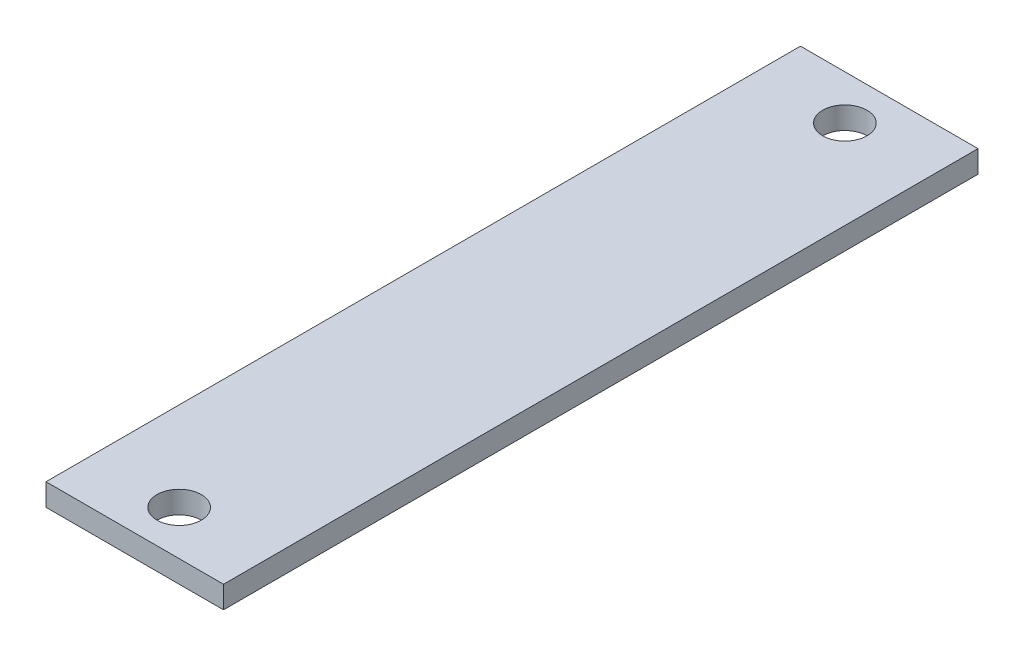
SolidWorks part; units mm, degrees
ref_plane "Front Plane" through (0, 0, 0) normal (0, 0, 1) x (1, 0, 0)
ref_plane "Top Plane" through (0, 0, 0) normal (0, 1, 0) x (1, 0, 0)
ref_plane "Right Plane" through (0, 0, 0) normal (1, 0, 0) x (0, 0, -1)
ref_plane "Plane1" through (0, -3.175, 0) normal (0, -1, 0) x (1, 0, 0)
sketch "Sketch1" plane through (0, -3.175, 0) normal (0, -1, 0) x (1, 0, 0)
  line L0 (-13.3421, -56.2584) -> (12.0579, -56.2584)
  line L1 (12.0579, -56.2584) -> (12.0579, 51.6916)
  line L2 (12.0579, 51.6916) -> (-13.3421, 51.6916)
  line L3 (-13.3421, 51.6916) -> (-13.3421, -56.2584)
  circle A0 centre (-0.6421, -49.9084) radius 3.175
  circle A1 centre (-0.6421, 45.3416) radius 3.175
extrude "Boss-Extrude1" add sketch "Sketch1" against normal blind 3.175
